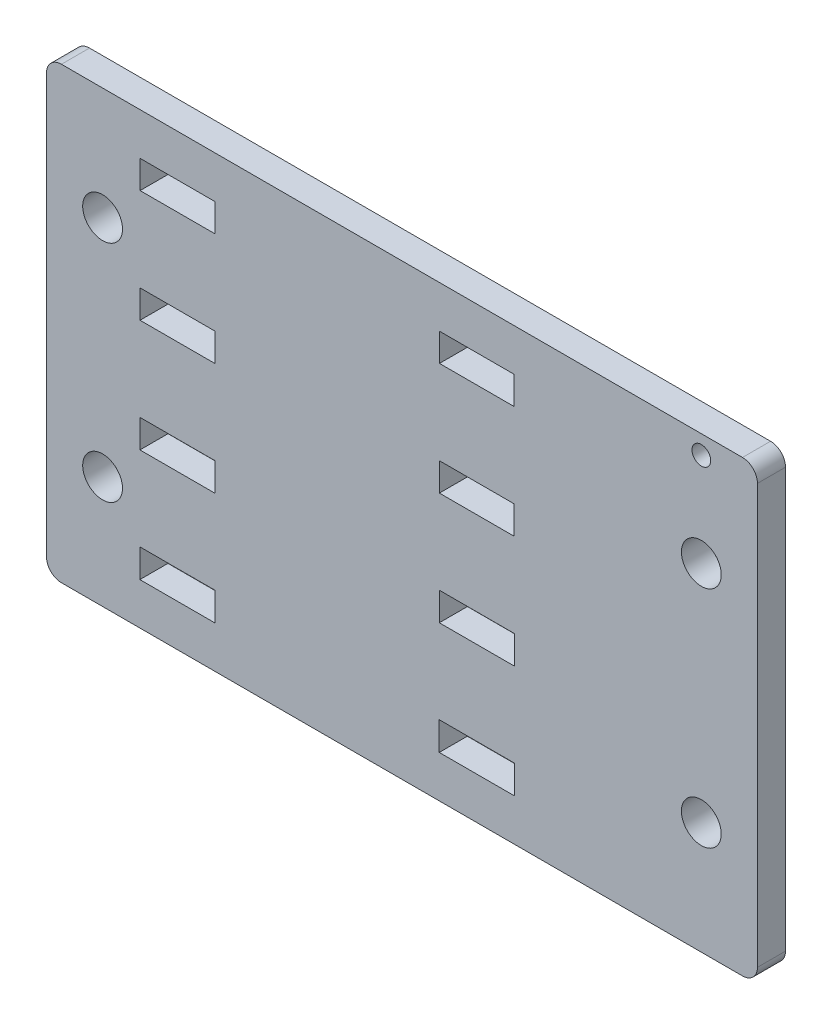
SolidWorks part; units mm, degrees
ref_plane "Front Plane" through (0, 0, 0) normal (0, 0, 1) x (1, 0, 0)
ref_plane "Top Plane" through (0, 0, 0) normal (0, 1, 0) x (1, 0, 0)
ref_plane "Right Plane" through (0, 0, 0) normal (1, 0, 0) x (0, 0, -1)
sketch "Sketch1" plane through (0, 0, 0) normal (0, 0, 1) x (1, 0, 0)
  line L1 (60.325, 38.1) -> (-60.325, 38.1)
  line L2 (60.325, 38.1) -> (60.325, -38.1)
  line L3 (60.325, -38.1) -> (-60.325, -38.1)
  line L4 (-60.325, 38.1) -> (-60.325, -38.1)
  line L5 (60.325, 38.1) -> (-60.325, -38.1) construction
  line L6 (60.325, -38.1) -> (-60.325, 38.1) construction
  point P0 (0, 0)
  dimension "D1" = 120.65
  dimension "D2" = 76.2
extrude "Boss-Extrude1" add sketch "Sketch1" along normal blind 4.7625
sketch "Sketch2" plane through (0, 0, 4.7625) normal (0, 0, 1) x (1, 0, 0)
  line L0 (-38.1, 38.1) -> (-38.1, -38.1) construction
  line L1 (60.325, 38.1) -> (-60.325, 38.1) construction
  line L2 (-60.325, -38.1) -> (60.325, -38.1) construction
  line L3 (12.7, 38.1) -> (12.7, -38.1) construction
  line L5 (57.15, 38.1) -> (-57.15, 38.1) construction
  line L6 (57.15, 38.1) -> (57.15, -38.1) construction
  line L7 (57.15, -38.1) -> (-57.15, -38.1) construction
  line L8 (-57.15, 38.1) -> (-57.15, -38.1) construction
  line L9 (57.15, 38.1) -> (-57.15, -38.1) construction
  line L10 (57.15, -38.1) -> (-57.15, 38.1) construction
  line L11 (-31.7627, 30.9436) -> (-44.4373, 30.9436)
  line L12 (-31.7627, 30.9436) -> (-31.7627, 26.2065)
  line L13 (-31.7627, 26.2065) -> (-44.4373, 26.2065)
  line L14 (-44.4373, 30.9436) -> (-44.4373, 26.2065)
  line L15 (-31.7627, 30.9436) -> (-44.4373, 26.2065) construction
  line L16 (-31.7627, 26.2065) -> (-44.4373, 30.9436) construction
  line L17 (19.0373, 30.9436) -> (6.3627, 30.9436)
  line L18 (19.0373, 30.9436) -> (19.0373, 26.2065)
  line L19 (19.0373, 26.2065) -> (6.3627, 26.2065)
  line L20 (6.3627, 30.9436) -> (6.3627, 26.2065)
  line L21 (19.0373, 30.9436) -> (6.3627, 26.2065) construction
  line L22 (19.0373, 26.2065) -> (6.3627, 30.9436) construction
  line L23 (-31.75, 11.9063) -> (-44.45, 11.9063)
  line L24 (-31.75, 11.9063) -> (-31.75, 7.1438)
  line L25 (-31.75, 7.1438) -> (-44.45, 7.1438)
  line L26 (-44.45, 11.9063) -> (-44.45, 7.1438)
  line L27 (-31.75, 11.9063) -> (-44.45, 7.1438) construction
  line L28 (-31.75, 7.1438) -> (-44.45, 11.9063) construction
  line L29 (19.05, 11.9063) -> (6.35, 11.9063)
  line L30 (19.05, 11.9063) -> (19.05, 7.1438)
  line L31 (19.05, 7.1438) -> (6.35, 7.1438)
  line L32 (6.35, 11.9063) -> (6.35, 7.1438)
  line L33 (19.05, 11.9063) -> (6.35, 7.1438) construction
  line L34 (19.05, 7.1438) -> (6.35, 11.9063) construction
  line L35 (-31.7373, -7.131) -> (-44.4627, -7.131)
  line L36 (-31.7373, -7.131) -> (-31.7373, -11.9189)
  line L37 (-31.7373, -11.9189) -> (-44.4627, -11.9189)
  line L38 (-44.4627, -7.131) -> (-44.4627, -11.9189)
  line L39 (-31.7373, -7.131) -> (-44.4627, -11.9189) construction
  line L40 (-31.7373, -11.9189) -> (-44.4627, -7.131) construction
  line L41 (19.0627, -7.131) -> (6.3373, -7.131)
  line L42 (19.0627, -7.131) -> (19.0627, -11.9189)
  line L43 (19.0627, -11.9189) -> (6.3373, -11.9189)
  line L44 (6.3373, -7.131) -> (6.3373, -11.9189)
  line L45 (19.0627, -7.131) -> (6.3373, -11.9189) construction
  line L46 (19.0627, -11.9189) -> (6.3373, -7.131) construction
  line L47 (-31.7246, -26.1683) -> (-44.4754, -26.1683)
  line L48 (-31.7246, -26.1683) -> (-31.7246, -30.9816)
  line L49 (-31.7246, -30.9816) -> (-44.4754, -30.9816)
  line L50 (-44.4754, -26.1683) -> (-44.4754, -30.9816)
  line L51 (-31.7246, -26.1683) -> (-44.4754, -30.9816) construction
  line L52 (-31.7246, -30.9816) -> (-44.4754, -26.1683) construction
  line L53 (19.0754, -26.1683) -> (6.3246, -26.1683)
  line L54 (19.0754, -26.1683) -> (19.0754, -30.9816)
  line L55 (19.0754, -30.9816) -> (6.3246, -30.9816)
  line L56 (6.3246, -26.1683) -> (6.3246, -30.9816)
  line L57 (19.0754, -26.1683) -> (6.3246, -30.9816) construction
  line L58 (19.0754, -30.9816) -> (6.3246, -26.1683) construction
  point P8 (0, 0)
  point P14 (-38.1, 28.575)
  point P19 (12.7, 28.575)
  point P24 (-38.1, 9.525)
  point P29 (12.7, 9.525)
  point P34 (-38.1, -9.525)
  point P39 (12.7, -9.525)
  point P44 (-38.1, -28.575)
  point P49 (12.7, -28.575)
  dimension "D1" = 114.3
  dimension "D2" = 19.05
  dimension "D3" = 50.8
  dimension "D4" = 12.6746
  dimension "D5" = 12.6746
  dimension "D6" = 4.7371
  dimension "D7" = 4.7371
  dimension "D8" = 9.525
  dimension "D9" = 9.525
  dimension "D10" = 12.7
  dimension "D11" = 4.7625
  dimension "D12" = 19.05
  dimension "D13" = 12.7
  dimension "D14" = 4.7625
  dimension "D15" = 19.05
  dimension "D16" = 12.7254
  dimension "D17" = 4.7879
  dimension "D18" = 12.7254
  dimension "D19" = 4.7879
  dimension "D20" = 19.05
  dimension "D21" = 19.05
  dimension "D22" = 12.7508
  dimension "D23" = 4.8133
  dimension "D24" = 19.05
  dimension "D25" = 12.7508
  dimension "D26" = 4.8133
  dimension "D27" = 19.05
extrude "Cut-Extrude1" cut sketch "Sketch2" against normal through all
hole_wizard "1/4 Clearance Hole1" positions "Sketch5" profile "Sketch4" hole size "1/4" standard "Ansi Inch"
sketch "Sketch5" plane through (0, 0, 4.7625) normal (0, 0, 1) x (1, 0, 0)
  line L0 (-60.325, 19.05) -> (60.325, 19.05) construction
  line L1 (-60.325, 38.1) -> (-60.325, -38.1) construction
  line L2 (60.325, -38.1) -> (60.325, 38.1) construction
  line L4 (-60.325, -19.05) -> (60.325, -19.05) construction
  line L6 (-44.4373, 30.9436) -> (-44.4373, 26.2065) construction
  line L7 (-44.4627, -7.131) -> (-44.4627, -11.9189) construction
  point P0 (-50.8, 19.05)
  point P1 (50.8, 19.05)
  point P3 (-50.8, -19.05)
  point P5 (50.8, -19.05)
  point P20 (-44.4373, 28.575)
  point P23 (-44.4627, -9.525)
  dimension "D1" = 9.525
  dimension "D2" = 9.525
  dimension "D3" = 9.525
  dimension "D4" = 9.525
  dimension "D5" = 9.525
  dimension "D6" = 9.525
sketch "Sketch4" plane through (-50.8, 19.05, 4.7625) normal (1, 0, 0) x (0, -1, 0)
  line L0 (0, 0) -> (0, 27.4298)
  line L1 (0, 27.4298) -> (3.3782, 25.4)
  line L2 (3.3782, 25.4) -> (3.3782, 0)
  line L5 (3.3782, 0) -> (0, 0)
  line L10 (0, 27.4298) -> (-3.3782, 25.4) construction
  line L11 (0, -6.35) -> (0, 107.95) construction
  dimension "Hole Dia." = 6.7564
  dimension "Hole Depth" = 25.4
  dimension "Drill Angle" = 118
sketch "Sketch6" plane through (0, 0, 4.7625) normal (0, 0, 1) x (1, 0, 0)
  line L0 (50.8, 38.1) -> (50.8, -38.1) construction
  line L1 (60.325, 38.1) -> (-60.325, 38.1) construction
  line L2 (-60.325, -38.1) -> (60.325, -38.1) construction
  circle A0 centre (50.8, 34.925) radius 1.5875
  dimension "D3" = 3.175
  dimension "D1" = 9.525
  dimension "D2" = 34.925
extrude "Cut-Extrude2" cut sketch "Sketch6" against normal through all
fillet "Fillet1" radius 2.54 4 edges at (60.325, 38.1, 2.3813) (60.325, -38.1, 2.3813) (-60.325, -38.1, 2.3813) (-60.325, 38.1, 2.3813)
